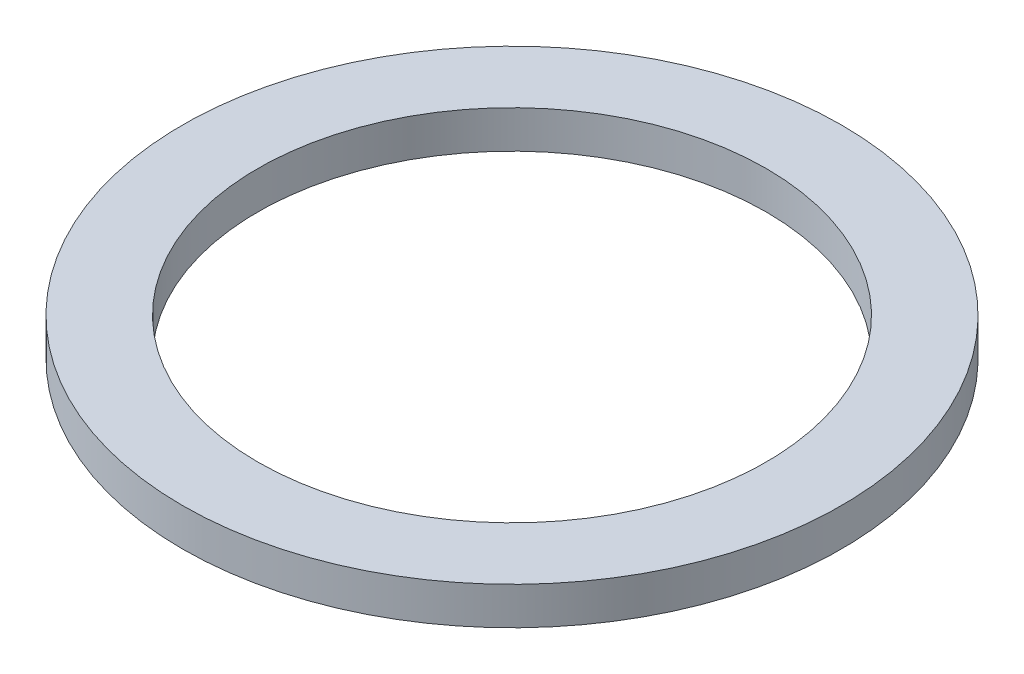
SolidWorks part; units mm, degrees
material "NBR"
ref_plane "Front Plane" through (0, 0, 0) normal (0, 0, 1) x (1, 0, 0)
ref_plane "Top Plane" through (0, 0, 0) normal (0, 1, 0) x (1, 0, 0)
ref_plane "Right Plane" through (0, 0, 0) normal (1, 0, 0) x (0, 0, -1)
sketch "Sketch1" plane through (0, 0, 0) normal (0, 1, 0) x (1, 0, 0)
  circle A0 centre (0, 0) radius 3.429
  circle A1 centre (0, 0) radius 4.445
  dimension "D2" = 8.89
  dimension "D1" = 1.016
extrude "Boss-Extrude1" add sketch "Sketch1" along normal blind 0.508
equation "\"w\"= 0.04"
equation "\"D1@Sketch1\"=\"w\""
equation "\"D2@Sketch1\"= .37 - .02 '20 thou smaller than channel diam"
